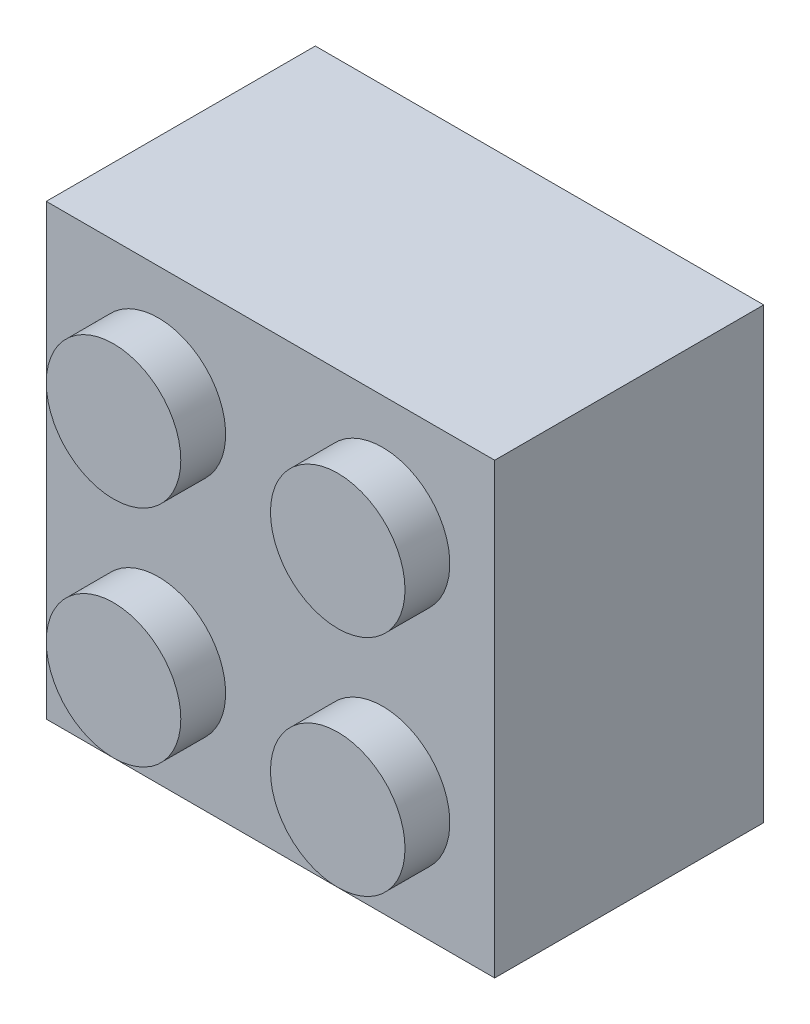
SolidWorks part; units mm, degrees
ref_plane "Front Plane" through (0, 0, 0) normal (0, 0, 1) x (1, 0, 0)
ref_plane "Top Plane" through (0, 0, 0) normal (0, 1, 0) x (1, 0, 0)
ref_plane "Right Plane" through (0, 0, 0) normal (1, 0, 0) x (0, 0, -1)
sketch "Sketch1" plane through (0, 0, 0) normal (0, 0, 1) x (1, 0, 0)
  line L1 (0, 0) -> (15.875, 0)
  line L2 (0, 0) -> (0, 15.875)
  line L3 (0, 15.875) -> (15.875, 15.875)
  line L4 (15.875, 0) -> (15.875, 15.875)
  dimension "D1" = 15.875
  dimension "D2" = 15.875
extrude "Boss-Extrude1" add sketch "Sketch1" along normal blind 9.525
sketch "Sketch2" plane through (0, 0, 9.525) normal (0, 0, 1) x (1, 0, 0)
  line L0 (0, 15.875) -> (0, 0) construction
  line L1 (15.875, 15.875) -> (0, 15.875) construction
  circle A0 centre (3.9688, 11.9062) radius 2.3813
  dimension "D1" = 4.7625
  dimension "D2" = 3.9688
  dimension "D3" = 3.9688
extrude "Boss-Extrude2" add sketch "Sketch2" along normal blind 1.5875
pattern_linear "LPattern1" count 2 spacing 7.9375 along (0, -1, 0) count 2 spacing 7.9375 along (1, 0, 0) of "Boss-Extrude2"
shell "Shell1" thickness 1.5875
sketch "Sketch3" plane through (0, 0, 7.9375) normal (0, 0, -1) x (-1, 0, 0)
  line L0 (-15.875, 0) -> (-15.875, 15.875) construction
  line L1 (-15.875, 15.875) -> (0, 15.875) construction
  circle A0 centre (-7.9375, 7.9375) radius 3.175
  circle A1 centre (-7.9375, 7.9375) radius 2.3813
  point P2 (-15.875, 7.9375)
  dimension "D1" = 6.35
  dimension "D4" = 4.7625
  dimension "D2" = 7.9375
  dimension "D3" = 7.9375
extrude "Boss-Extrude9" add sketch "Sketch3" along normal blind 7.9375
